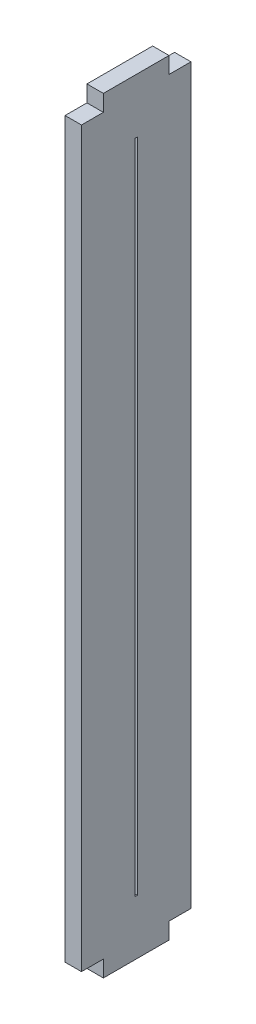
SolidWorks part; units mm, degrees
ref_plane "Front Plane" through (0, 0, 0) normal (0, 0, 1) x (1, 0, 0)
ref_plane "Top Plane" through (0, 0, 0) normal (0, 1, 0) x (1, 0, 0)
ref_plane "Right Plane" through (0, 0, 0) normal (1, 0, 0) x (0, 0, -1)
sketch "Sketch1" plane through (0, 0, 0) normal (1, 0, 0) x (0, 0, -1)
  line L1 (-10, -30.8442) -> (0, -30.8442)
  line L2 (-10, -30.8442) -> (-10, 39.1558)
  line L3 (-10, 39.1558) -> (0, 39.1558)
  line L4 (0, -30.8442) -> (0, 39.1558)
  dimension "D1" = 70
  dimension "D2" = 10
extrude "Boss-Extrude1" add sketch "Sketch1" along normal blind 1.5
sketch "Sketch2" plane through (1.5, 0, 0) normal (1, 0, 0) x (0, 0, -1)
  line L0 (0, 39.1558) -> (-10, 39.1558) construction
  line L1 (-8, 39.1558) -> (-10, 39.1558)
  line L2 (-8, 39.1558) -> (-8, 37.6558)
  line L3 (-8, 37.6558) -> (-10, 37.6558)
  line L4 (-10, 39.1558) -> (-10, 37.6558)
  line L5 (-10, 39.1558) -> (-10, -30.8442) construction
  line L6 (0, -30.8442) -> (0, 39.1558) construction
  line L7 (-2, 39.1558) -> (0, 39.1558)
  line L8 (-2, 39.1558) -> (-2, 37.6558)
  line L9 (-2, 37.6558) -> (0, 37.6558)
  line L10 (0, 39.1558) -> (0, 37.6558)
  line L11 (-10, -30.8442) -> (0, -30.8442) construction
  line L12 (-2, -30.8442) -> (0, -30.8442)
  line L13 (-2, -30.8442) -> (-2, -29.3442)
  line L14 (-2, -29.3442) -> (0, -29.3442)
  line L15 (0, -30.8442) -> (0, -29.3442)
  line L17 (-8, -30.8442) -> (-10, -30.8442)
  line L18 (-8, -30.8442) -> (-8, -29.3442)
  line L19 (-8, -29.3442) -> (-10, -29.3442)
  line L20 (-10, -30.8442) -> (-10, -29.3442)
  dimension "D1" = 1.5
  dimension "D2" = 2
  dimension "D3" = 2
  dimension "D4" = 1.5
extrude "Cut-Extrude1" cut sketch "Sketch2" against normal blind 10
sketch "Sketch3" plane through (1.5, 0, 0) normal (1, 0, 0) x (0, 0, -1)
  line L1 (-5.1, 34.1558) -> (-4.9, 34.1558)
  line L2 (-5.1, 34.1558) -> (-5.1, -25.8442)
  line L3 (-5.1, -25.8442) -> (-4.9, -25.8442)
  line L4 (-4.9, 34.1558) -> (-4.9, -25.8442)
  line L6 (-10, 37.6558) -> (-10, -29.3442) construction
  line L7 (0, -29.3442) -> (0, 37.6558) construction
  line L8 (-8, -30.8442) -> (-2, -30.8442) construction
  line L9 (-2, 39.1558) -> (-8, 39.1558) construction
  dimension "D1" = 4.9
  dimension "D2" = 4.9
  dimension "D3" = 5
  dimension "D4" = 5
extrude "Cut-Extrude2" cut sketch "Sketch3" against normal blind 10
